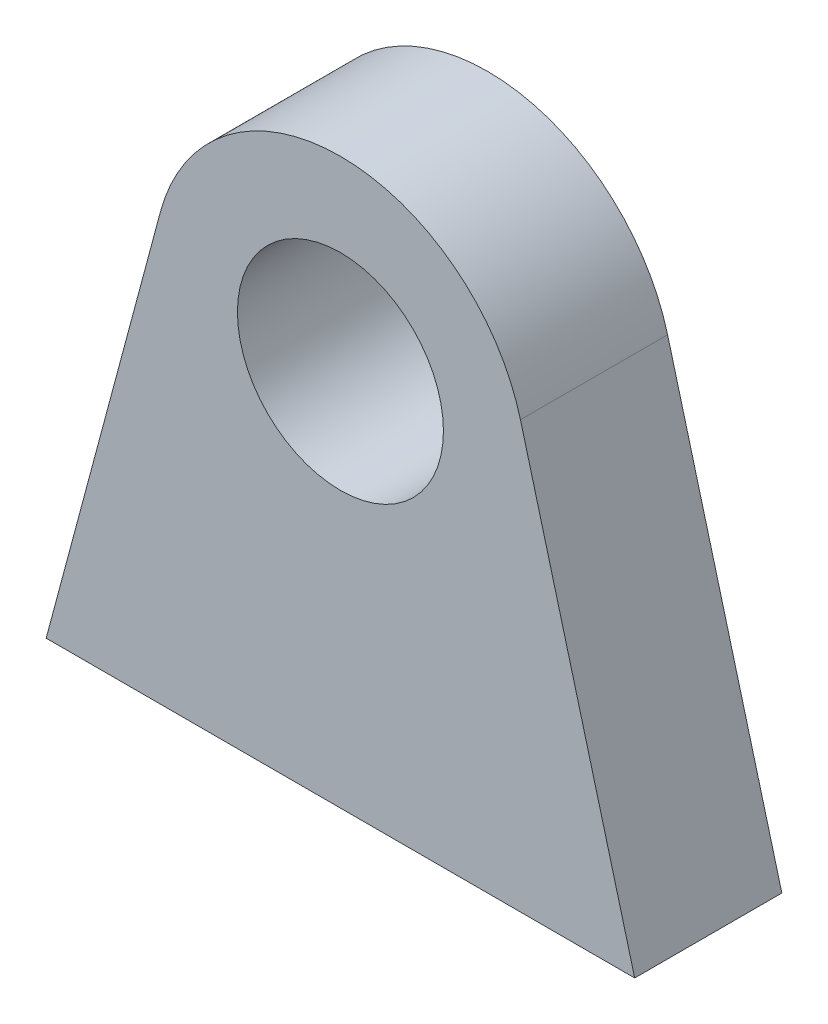
SolidWorks part; units mm, degrees
ref_plane "前视基准面" through (0, 0, 0) normal (0, 0, 1) x (1, 0, 0)
ref_plane "上视基准面" through (0, 0, 0) normal (0, 1, 0) x (1, 0, 0)
ref_plane "右视基准面" through (0, 0, 0) normal (1, 0, 0) x (0, 0, -1)
other "Configuration Table"
sketch "草图1" plane through (0, 0, 0) normal (0, 0, 1) x (1, 0, 0)
  line L0 (-20, 0) -> (20, 0)
  line L1 (-20, 0) -> (-12.2354, 28.9778)
  line L3 (0, -15.9378) -> (0, 15.9378) construction
  line L4 (20, 0) -> (12.2354, 28.9778)
  arc A0 (-12.2354, 28.9778) -> (12.2354, 28.9778) centre (0, 25.6993) cw
  dimension "D1" = 40
  dimension "D2" = 75
  dimension "D3" = 30
extrude "凸台-拉伸1" add sketch "草图1" along normal blind 10
sketch "草图2" plane through (0, 0, 0) normal (0, 0, 1) x (1, 0, 0)
  circle A0 centre (0, 25.6993) radius 7
  arc A1 (12.2354, 28.9778) -> (-12.2354, 28.9778) centre (0, 25.6993) ccw construction
  dimension "D1" = 14
extrude "切除-拉伸1" cut sketch "草图2" along normal blind 10
